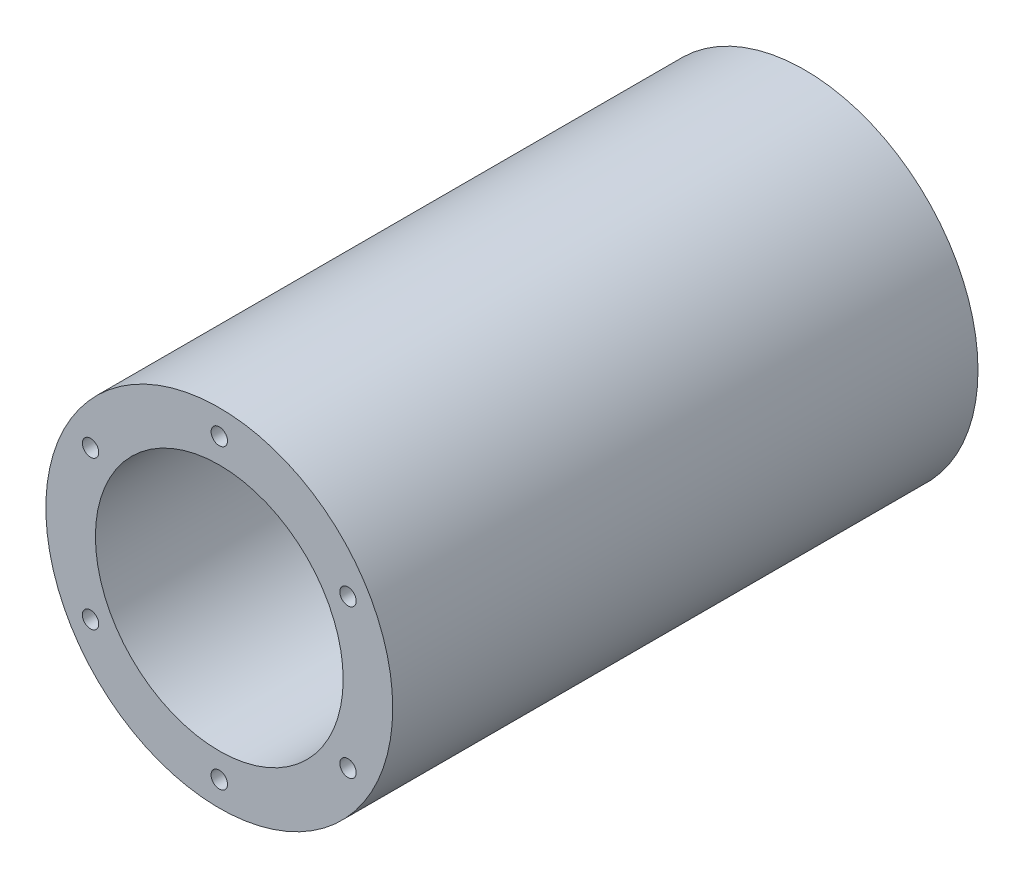
SolidWorks part; units mm, degrees
ref_plane "Front" through (0, 0, 0) normal (0, 0, 1) x (1, 0, 0)
ref_plane "Top" through (0, 0, 0) normal (0, 1, 0) x (1, 0, 0)
ref_plane "Right" through (0, 0, 0) normal (1, 0, 0) x (0, 0, -1)
sketch "Sketch1" plane through (0, 0, 0) normal (0, 0, 1) x (1, 0, 0)
  circle A0 centre (0, 0) radius 44.45
  circle A1 centre (0, 0) radius 31.75
  dimension "D1" = 88.9
  dimension "D2" = 63.5
extrude "Boss-Extrude1" add sketch "Sketch1" along normal mid plane 150
sketch "Sketch2" plane through (0, 0, 75) normal (0, 0, 1) x (1, 0, 0)
  line L0 (0, 0) -> (0, 31.75) construction
  line L1 (0, 31.75) -> (0, 44.45) construction
  circle A0 centre (0, 0) radius 31.75 construction
  circle A1 centre (0, 0) radius 44.45 construction
  circle A2 centre (0, 38.1) radius 2.5
  dimension "D1" = 5
hole_wizard "M5x0.8 Tapped Hole1" positions "3DSketch1" profile "Sketch3" tap size "M5x0.8" standard "ANSI Metric"
sketch3d "3DSketch1"
  point P0 (0, 38.1, 75)
sketch "Sketch3" plane through (0, 38.1, 75) normal (1, 0, 0) x (0, -1, 0)
  line L0 (0, 0) -> (0, 13.6618)
  line L1 (0, 13.6618) -> (2.1, 12.4)
  line L2 (2.1, 12.4) -> (2.1, 0)
  line L5 (2.1, 0) -> (0, 0)
  line L10 (0, 13.6618) -> (-2.1, 12.4) construction
  line L11 (0, -6.35) -> (0, 107.95) construction
  dimension "Tap Drill Dia." = 4.2
  dimension "Tap Drill Depth" = 12.4
  dimension "Drill Angle" = 118
cosmetic thread "Hole Thread1" parameters "D1"=10, "D2"=5
pattern_circular "CirPattern1" count 6 over 360 about axis through (0, 0, 0) along (0, 0, 1) of "M5x0.8 Tapped Hole1"
cosmetic thread "Hole Thread2" parameters "D1"=10, "D2"=5
cosmetic thread "Hole Thread3" parameters "D1"=10, "D2"=5
cosmetic thread "Hole Thread4" parameters "D1"=10, "D2"=5
cosmetic thread "Hole Thread5" parameters "D1"=10, "D2"=5
cosmetic thread "Hole Thread6" parameters "D1"=10, "D2"=5
mirror "Mirror1" about plane through (0, 0, 0) normal (0, 0, 1) of "CirPattern1", "M5x0.8 Tapped Hole1"
cosmetic thread "Hole Thread7" parameters "D1"=10, "D2"=5
cosmetic thread "Hole Thread8" parameters "D1"=10, "D2"=5
cosmetic thread "Hole Thread9" parameters "D1"=10, "D2"=5
cosmetic thread "Hole Thread10" parameters "D1"=10, "D2"=5
cosmetic thread "Hole Thread11" parameters "D1"=10, "D2"=5
cosmetic thread "Hole Thread12" parameters "D1"=10, "D2"=5
ref_plane "Plane1" through (-44.45, 0, 0) normal (-1, 0, 0) x (0, 0, 1)
sketch "Sketch4" [suppressed] plane through (-44.45, 0, 0) normal (-1, 0, 0) x (0, 0, 1)
  line L0 (0, 0) -> (-60, 0) construction
  line L2 (-66.35, -9.525) -> (-53.65, -9.525)
  line L3 (-66.35, -9.525) -> (-66.35, 9.525)
  line L4 (-66.35, 9.525) -> (-53.65, 9.525)
  line L5 (-53.65, -9.525) -> (-53.65, 9.525)
  line L6 (-66.35, -9.525) -> (-53.65, 9.525) construction
  line L7 (-66.35, 9.525) -> (-53.65, -9.525) construction
  circle A0 centre (-60, 0) radius 6.35 construction
  dimension "D1" = 12.7
  dimension "D2" = 60
  dimension "D3" = 19.05
extrude "Cut-Extrude2" [suppressed] cut sketch "Sketch4" against normal blind 1
sketch "Sketch5" [suppressed] plane through (-44.45, 0, 0) normal (-1, 0, 0) x (0, 0, 1)
  circle A0 centre (-60, 0) radius 6.35 construction
  circle A1 centre (-60, 0) radius 6.35
extrude "Cut-Extrude3" [suppressed] cut sketch "Sketch5" against normal blind 22
